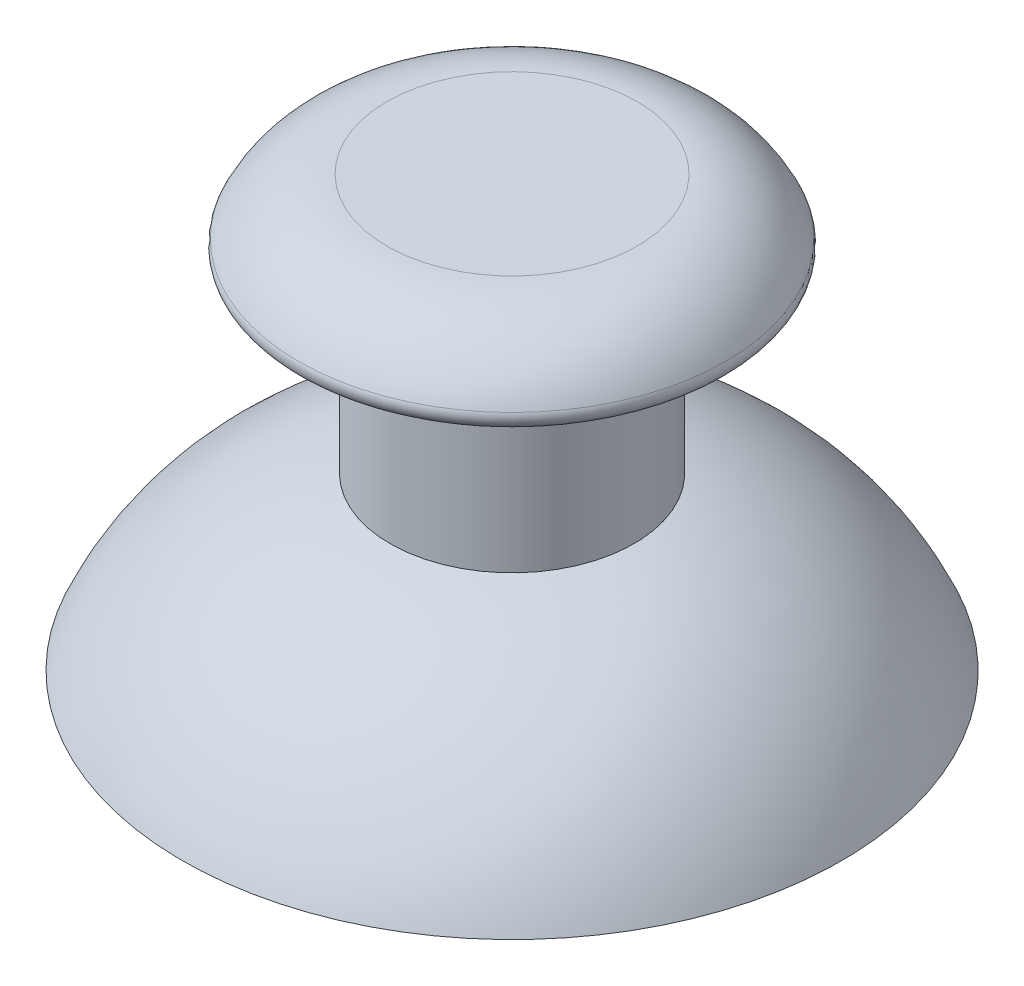
SolidWorks part; units mm, degrees
ref_plane "Front Plane" through (0, 0, 0) normal (0, 0, 1) x (1, 0, 0)
ref_plane "Top Plane" through (0, 0, 0) normal (0, 1, 0) x (1, 0, 0)
ref_plane "Right Plane" through (0, 0, 0) normal (1, 0, 0) x (0, 0, -1)
sketch "Sketch1" plane through (0, 0, 0) normal (0, 0, 1) x (1, 0, 0)
  line L0 (0, 31.6179) -> (0, 20.0224)
  line L1 (-12.4026, 14) -> (-13.5, 14)
  line L2 (-5, 21) -> (-5, 28.6179)
  line L3 (-5, 28.6179) -> (-9, 28.6179)
  line L4 (0, 31.6179) -> (-5.127, 31.6179)
  line L5 (-4.7893, 20.0224) -> (0, 20.0224)
  arc A0 (-13.5, 14) -> (-5, 21) centre (-2.4718, 9.2693) cw
  arc A1 (-9, 28.6179) -> (-5.127, 31.6179) centre (-5.127, 27.6179) cw
  arc A2 (-12.4026, 14) -> (-4.7893, 20.0224) centre (-2.4718, 9.2693) cw
  arc A3 (-12.581, 13.6058) -> (-4.7893, 20.0224) centre (-2.4718, 9.2693) cw construction
  dimension "D5" = 12
  dimension "D1" = 7
  dimension "D2" = 14
  dimension "D3" = 5
  dimension "D4" = 9
  dimension "D7" = 3
  dimension "D9" = 1
revolve "Revolve1" add sketch "Sketch1" angle 360 about L0
fillet "Fillet1" radius 0.5 1 edges at (-9, 28.6179, 0)
sketch "Sketch2" plane through (0, 31.6179, 0) normal (0, 1, 0) x (1, 0, 0)
  line L0 (0, 5.127) -> (0, -5.127)
  circle A0 centre (0, 0) radius 5.127 construction
